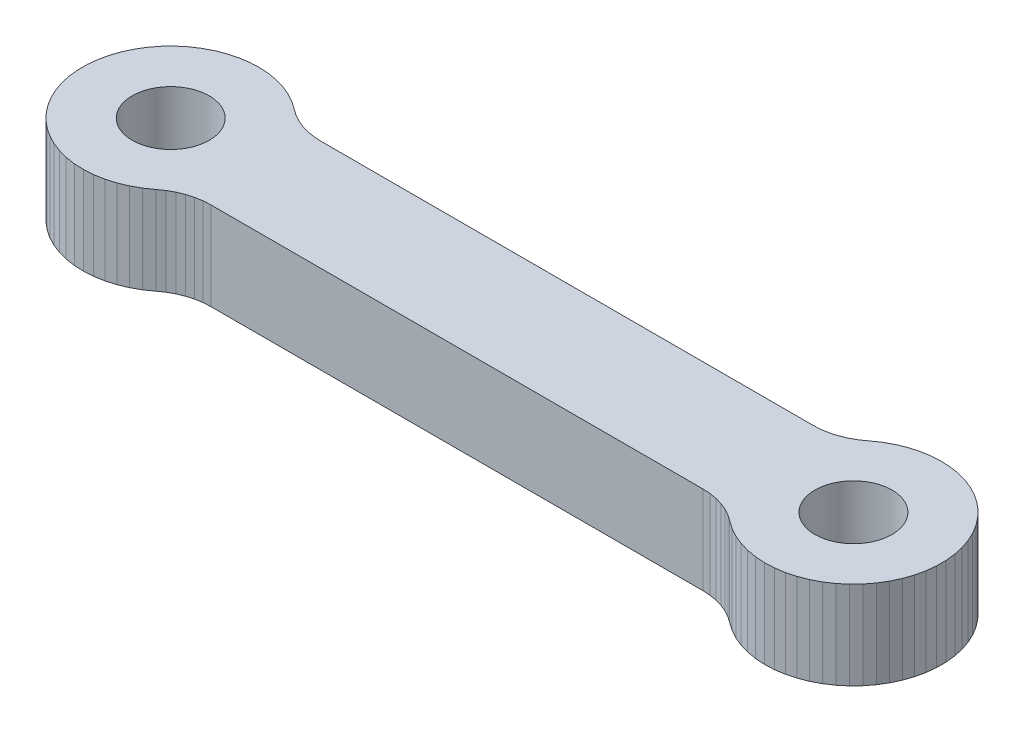
SolidWorks part; units mm, degrees
ref_plane "Front Plane" through (0, 0, 0) normal (0, 0, 1) x (1, 0, 0)
ref_plane "Top Plane" through (0, 0, 0) normal (0, 1, 0) x (1, 0, 0)
ref_plane "Right Plane" through (0, 0, 0) normal (1, 0, 0) x (0, 0, -1)
ref_plane "Plane1" through (0, 4, 0) normal (0, 1, 0) x (1, 0, 0)
sketch "Sketch1" plane through (0, 4, 0) normal (0, 1, 0) x (1, 0, 0)
  line L76 (32.5256, -7.1429) -> (32.8828, -7.3937)
  line L77 (32.8828, -7.3937) -> (33.2651, -7.6042)
  line L78 (33.2651, -7.6042) -> (33.668, -7.7717)
  line L79 (33.668, -7.7717) -> (34.0869, -7.8944)
  line L80 (34.0869, -7.8944) -> (34.5166, -7.9707)
  line L81 (34.5166, -7.9707) -> (34.952, -7.9997)
  line L82 (34.952, -7.9997) -> (35.388, -7.9811)
  line L83 (35.388, -7.9811) -> (35.8194, -7.9152)
  line L84 (35.8194, -7.9152) -> (36.2411, -7.8026)
  line L85 (36.2411, -7.8026) -> (36.648, -7.6448)
  line L86 (36.648, -7.6448) -> (37.0352, -7.4435)
  line L87 (37.0352, -7.4435) -> (37.3982, -7.2013)
  line L88 (37.3982, -7.2013) -> (37.7327, -6.921)
  line L89 (37.7327, -6.921) -> (38.0347, -6.6059)
  line L90 (38.0347, -6.6059) -> (38.3005, -6.2598)
  line L91 (38.3005, -6.2598) -> (38.527, -5.8868)
  line L92 (38.527, -5.8868) -> (38.7116, -5.4913)
  line L93 (38.7116, -5.4913) -> (38.852, -5.0781)
  line L94 (38.852, -5.0781) -> (38.9465, -4.652)
  line L95 (38.9465, -4.652) -> (38.9941, -4.2182)
  line L96 (38.9941, -4.2182) -> (38.9941, -3.7818)
  line L97 (38.9941, -3.7818) -> (38.9465, -3.348)
  line L98 (38.9465, -3.348) -> (38.852, -2.9219)
  line L99 (38.852, -2.9219) -> (38.7116, -2.5087)
  line L100 (38.7116, -2.5087) -> (38.527, -2.1132)
  line L101 (38.527, -2.1132) -> (38.3005, -1.7402)
  line L102 (38.3005, -1.7402) -> (38.0347, -1.3941)
  line L103 (38.0347, -1.3941) -> (37.7327, -1.079)
  line L104 (37.7327, -1.079) -> (37.3982, -0.7987)
  line L105 (37.3982, -0.7987) -> (37.0352, -0.5565)
  line L106 (37.0352, -0.5565) -> (36.648, -0.3552)
  line L107 (36.648, -0.3552) -> (36.2411, -0.1974)
  line L108 (36.2411, -0.1974) -> (35.8194, -0.0848)
  line L109 (35.8194, -0.0848) -> (35.388, -0.0189)
  line L110 (35.388, -0.0189) -> (34.952, -0.0003)
  line L111 (34.952, -0.0003) -> (34.5166, -0.0293)
  line L112 (34.5166, -0.0293) -> (34.0869, -0.1056)
  line L113 (34.0869, -0.1056) -> (33.668, -0.2283)
  line L114 (33.668, -0.2283) -> (33.2651, -0.3958)
  line L115 (33.2651, -0.3958) -> (32.8828, -0.6063)
  line L116 (32.8828, -0.6063) -> (32.5256, -0.8571)
  line L117 (32.5256, -0.8571) -> (32.2527, -1.0485)
  line L118 (32.2527, -1.0485) -> (31.9602, -1.2083)
  line L119 (31.9602, -1.2083) -> (31.6519, -1.3347)
  line L120 (31.6519, -1.3347) -> (31.3313, -1.4262)
  line L121 (31.3313, -1.4262) -> (31.0027, -1.4815)
  line L122 (31.0027, -1.4815) -> (30.6699, -1.5)
  line L123 (30.6699, -1.5) -> (8.3301, -1.5)
  line L124 (8.3301, -1.5) -> (7.9973, -1.4815)
  line L125 (7.9973, -1.4815) -> (7.6687, -1.4262)
  line L126 (7.6687, -1.4262) -> (7.3481, -1.3347)
  line L127 (7.3481, -1.3347) -> (7.0398, -1.2083)
  line L128 (7.0398, -1.2083) -> (6.7473, -1.0485)
  line L129 (6.7473, -1.0485) -> (6.4744, -0.8571)
  line L130 (6.4744, -0.8571) -> (6.1172, -0.6063)
  line L131 (6.1172, -0.6063) -> (5.7349, -0.3958)
  line L132 (5.7349, -0.3958) -> (5.332, -0.2283)
  line L133 (5.332, -0.2283) -> (4.9131, -0.1056)
  line L134 (4.9131, -0.1056) -> (4.4834, -0.0293)
  line L135 (4.4834, -0.0293) -> (4.048, -0.0003)
  line L136 (4.048, -0.0003) -> (3.612, -0.0189)
  line L137 (3.612, -0.0189) -> (3.1806, -0.0848)
  line L138 (3.1806, -0.0848) -> (2.7589, -0.1974)
  line L139 (2.7589, -0.1974) -> (2.352, -0.3552)
  line L140 (2.352, -0.3552) -> (1.9648, -0.5565)
  line L141 (1.9648, -0.5565) -> (1.6018, -0.7987)
  line L142 (1.6018, -0.7987) -> (1.2673, -1.079)
  line L143 (1.2673, -1.079) -> (0.9653, -1.3941)
  line L144 (0.9653, -1.3941) -> (0.6995, -1.7402)
  line L145 (0.6995, -1.7402) -> (0.473, -2.1132)
  line L146 (0.473, -2.1132) -> (0.2884, -2.5087)
  line L147 (0.2884, -2.5087) -> (0.148, -2.9219)
  line L148 (0.148, -2.9219) -> (0.0535, -3.348)
  line L149 (0.0535, -3.348) -> (0.006, -3.7818)
  line L150 (0.006, -3.7818) -> (0.006, -4.2182)
  line L151 (0.006, -4.2182) -> (0.0535, -4.652)
  line L152 (0.0535, -4.652) -> (0.148, -5.0781)
  line L153 (0.148, -5.0781) -> (0.2884, -5.4913)
  line L154 (0.2884, -5.4913) -> (0.473, -5.8868)
  line L155 (0.473, -5.8868) -> (0.6995, -6.2598)
  line L156 (0.6995, -6.2598) -> (0.9653, -6.6059)
  line L157 (0.9653, -6.6059) -> (1.2673, -6.921)
  line L158 (1.2673, -6.921) -> (1.6018, -7.2013)
  line L159 (1.6018, -7.2013) -> (1.9648, -7.4435)
  line L160 (1.9648, -7.4435) -> (2.352, -7.6448)
  line L161 (2.352, -7.6448) -> (2.7589, -7.8026)
  line L162 (2.7589, -7.8026) -> (3.1806, -7.9152)
  line L163 (3.1806, -7.9152) -> (3.612, -7.9811)
  line L164 (3.612, -7.9811) -> (4.048, -7.9997)
  line L165 (4.048, -7.9997) -> (4.4834, -7.9707)
  line L166 (4.4834, -7.9707) -> (4.9131, -7.8944)
  line L167 (4.9131, -7.8944) -> (5.332, -7.7717)
  line L168 (5.332, -7.7717) -> (5.7349, -7.6042)
  line L169 (5.7349, -7.6042) -> (6.1172, -7.3937)
  line L170 (6.1172, -7.3937) -> (6.4744, -7.1429)
  line L171 (6.4744, -7.1429) -> (6.7473, -6.9515)
  line L172 (6.7473, -6.9515) -> (7.0398, -6.7917)
  line L173 (7.0398, -6.7917) -> (7.3481, -6.6653)
  line L174 (7.3481, -6.6653) -> (7.6687, -6.5738)
  line L175 (7.6687, -6.5738) -> (7.9973, -6.5185)
  line L176 (7.9973, -6.5185) -> (8.3301, -6.5)
  line L177 (8.3301, -6.5) -> (30.6699, -6.5)
  line L178 (30.6699, -6.5) -> (31.0027, -6.5185)
  line L179 (31.0027, -6.5185) -> (31.3313, -6.5738)
  line L180 (31.3313, -6.5738) -> (31.6519, -6.6653)
  line L181 (31.6519, -6.6653) -> (31.9602, -6.7917)
  line L182 (31.9602, -6.7917) -> (32.2527, -6.9515)
  line L183 (32.2527, -6.9515) -> (32.5256, -7.1429)
  circle A0 centre (4.0062, -3.9989) radius 1.75
  circle A2 centre (35, -4) radius 1.75
extrude "Boss-Extrude1" add sketch "Sketch1" against normal blind 4
